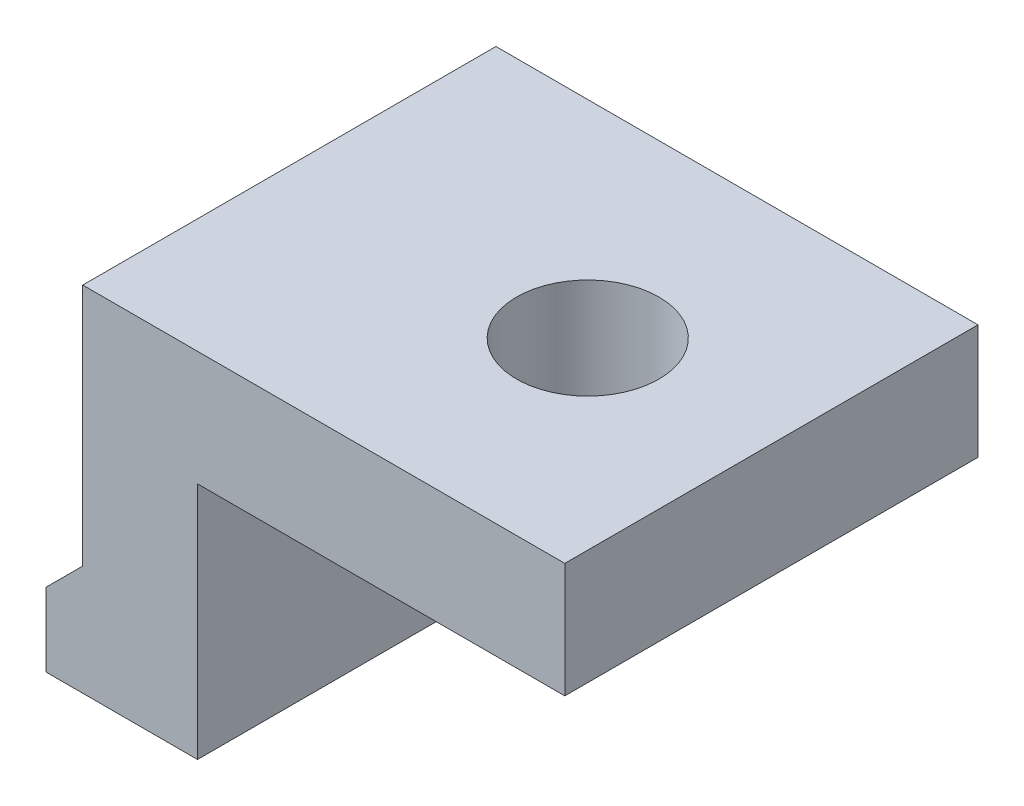
SolidWorks part; units mm, degrees
ref_plane "Front" through (0, 0, 0) normal (0, 0, 1) x (1, 0, 0)
ref_plane "Top" through (0, 0, 0) normal (0, 1, 0) x (1, 0, 0)
ref_plane "Right" through (0, 0, 0) normal (1, 0, 0) x (0, 0, -1)
sketch "Sketch1" plane through (0, 0, 0) normal (0, 0, 1) x (1, 0, 0)
  line L0 (-2.5, 0) -> (-2.5, -5.3)
  line L1 (-2.5, -5.3) -> (-3.3, -6.1)
  line L2 (-3.3, -6.1) -> (-3.3, -7.7)
  line L3 (-3.3, -7.7) -> (0, -7.7)
  line L4 (0, -7.7) -> (0, 0)
  line L5 (0, 0) -> (-2.5, 0)
  line L7 (0, 0) -> (8, 0)
  line L8 (0, 0) -> (0, -2.5)
  line L9 (0, -2.5) -> (8, -2.5)
  line L10 (8, 0) -> (8, -2.5)
  line L11 (0, 0) -> (8, -2.5) construction
  line L12 (0, -2.5) -> (8, 0) construction
  point P10 (4, -1.25)
  dimension "D1" = 5.3
  dimension "D2" = 135
  dimension "D3" = 1.6
  dimension "D4" = 0.8
  dimension "D5" = 2.5
  dimension "D6" = 2.5
  dimension "D7" = 8
extrude "Boss-Extrude1" add sketch "Sketch1" along normal blind 9 contours L10 L7 L4 L9 | L4 L5 L0 L1 L2 L3
sketch "Sketch2" plane through (0, -2.5, 0) normal (0, -1, 0) x (1, 0, 0)
  line L0 (0, 0) -> (8, 9) construction
  circle A0 centre (4, 4.5) radius 1.55
  dimension "D1" = 3.1
extrude "Cut-Extrude1" cut sketch "Sketch2" against normal through all
